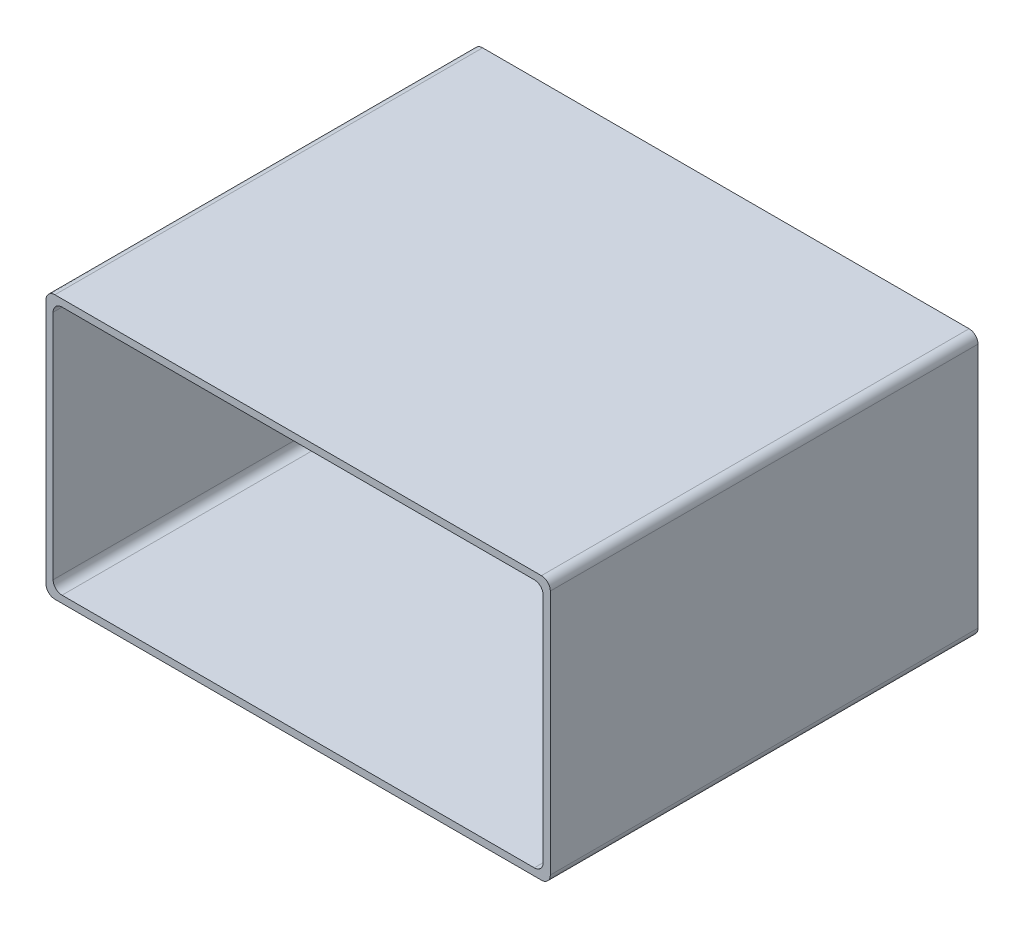
SolidWorks part; units mm, degrees
ref_plane "Plan de face" through (0, 0, 0) normal (0, 0, 1) x (1, 0, 0)
ref_plane "Plan de dessus" through (0, 0, 0) normal (0, 1, 0) x (1, 0, 0)
ref_plane "Plan de droite" through (0, 0, 0) normal (1, 0, 0) x (0, 0, -1)
sketch "Esquisse1" plane through (0, 0, 0) normal (0, 0, 1) x (1, 0, 0)
  line L0 (-28.3, 14.8) -> (28.3, 14.8)
  line L1 (-27.5, 14) -> (27.5, 14)
  line L2 (-27.5, 14) -> (-27.5, -14)
  line L3 (-27.5, -14) -> (27.5, -14)
  line L4 (27.5, 14) -> (27.5, -14)
  line L5 (-27.5, 14) -> (27.5, -14) construction
  line L6 (-27.5, -14) -> (27.5, 14) construction
  line L7 (28.3, 14.8) -> (28.3, -14.8)
  line L8 (-28.3, -14.8) -> (28.3, -14.8)
  line L9 (-28.3, 14.8) -> (-28.3, -14.8)
  point P0 (0, 0)
  dimension "D1" = 28
  dimension "D2" = 55
  dimension "D3" = 0.8
extrude "Boss.-Extru.1" add sketch "Esquisse1" along normal blind 48
fillet "Congé1" radius 1 8 edges at (-27.5, 14, 24) (-27.5, -14, 24) (27.5, -14, 24) (27.5, 14, 24) (28.3, -14.8, 24) (-28.3, -14.8, 24) (-28.3, 14.8, 24) (28.3, 14.8, 24)
